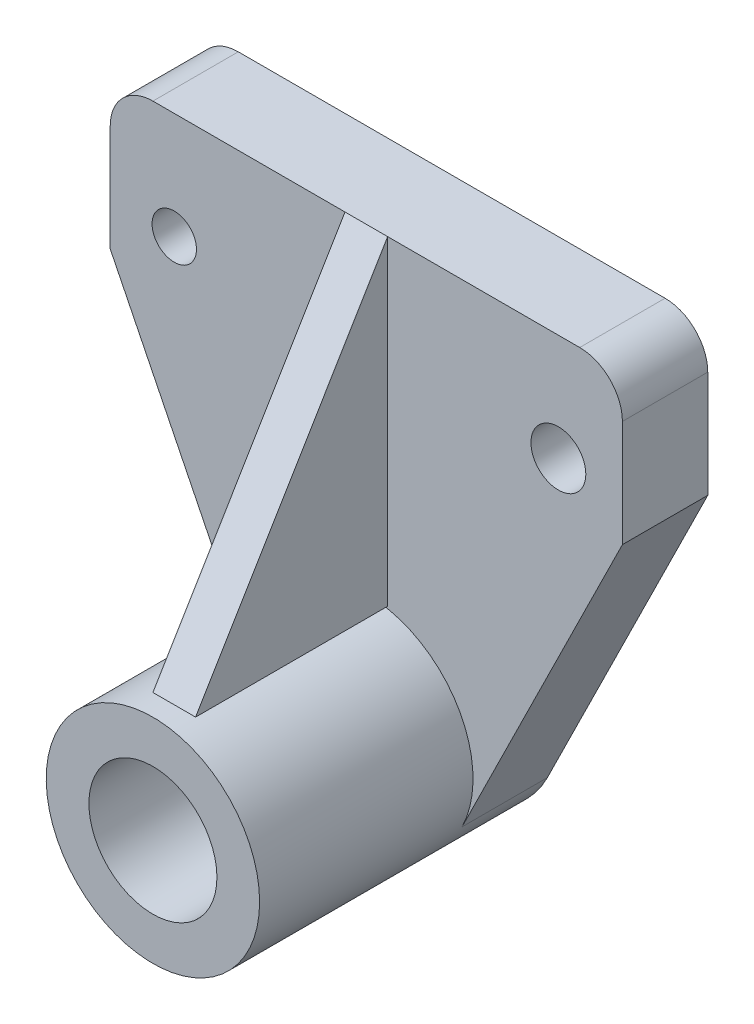
SolidWorks part; units mm, degrees
ref_plane "Front Plane" through (0, 0, 0) normal (0, 0, 1) x (1, 0, 0)
ref_plane "Top Plane" through (0, 0, 0) normal (0, 1, 0) x (1, 0, 0)
ref_plane "Right Plane" through (0, 0, 0) normal (1, 0, 0) x (0, 0, -1)
sketch "Sketch1" plane through (0, 0, 0) normal (0, 0, 1) x (1, 0, 0)
  line L0 (0, 101.9394) -> (0, -105.9699) construction
  line L1 (-134.3517, 0) -> (117.5577, 0) construction
  line L2 (-60, 71.7631) -> (60, 71.7631)
  line L4 (-60, 71.7631) -> (-60, 36.7631)
  line L5 (60, 71.7631) -> (60, 36.7631)
  line L6 (60, 36.7631) -> (22.4135, -39.3109)
  line L7 (-60, 36.7631) -> (-22.4135, -39.3109)
  arc A0 (-22.4135, -39.3109) -> (22.4135, -39.3109) centre (0, -28.2369) ccw
  circle A2 centre (-45, 46.7631) radius 5.1988
  circle A3 centre (45, 46.7631) radius 6.4293
  point P8 (0, 71.7631)
  dimension "D5" = 35
  dimension "D1" = 120
  dimension "D6" = 35
  dimension "D7" = 90
  dimension "D9" = 75
  dimension "D10" = 75
extrude "Boss-Extrude2" add sketch "Sketch1" along normal blind 20
sketch "Sketch2" plane through (0, 0, 20) normal (0, 0, 1) x (1, 0, 0)
  circle A0 centre (0, -28.2369) radius 25
  circle A1 centre (-45, 46.7631) radius 5.1988 construction
  dimension "D1" = 50
  dimension "D2" = 75
extrude "Boss-Extrude3" add sketch "Sketch2" along normal blind 50
sketch "Sketch3" plane through (0, 0, 70) normal (0, 0, 1) x (1, 0, 0)
  circle A0 centre (0, -28.2369) radius 15
  dimension "D1" = 30
extrude "Cut-Extrude1" cut sketch "Sketch3" against normal through all
sketch "Sketch4" plane through (0, 0, 0) normal (1, 0, 0) x (0, 0, -1)
  line L0 (-20, 71.7631) -> (-20, -3.2369)
  line L1 (-20, 36.7631) -> (-20, 71.7631) construction
  line L2 (-20, -3.2369) -> (-65, -3.2369)
  line L3 (-20, -3.2369) -> (-70, -3.2369) construction
  line L4 (-65, -3.2369) -> (-20, 71.7631)
  dimension "D1" = 45
  dimension "D2" = 75
extrude "Boss-Extrude5" add sketch "Sketch4" along normal mid plane 10 separate body
fillet "Fillet1" radius 10 2 edges at (-60, 71.7631, 10) (60, 71.7631, 10)
